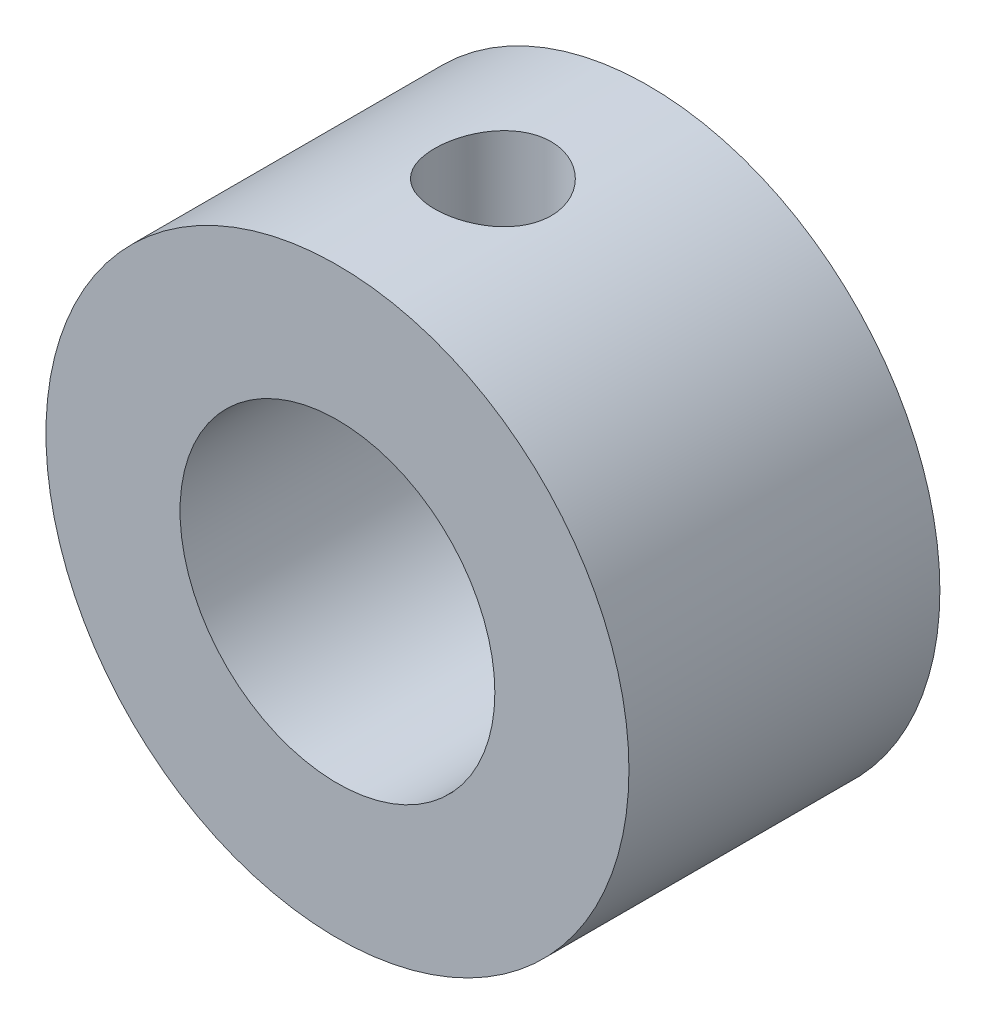
SolidWorks part; units mm, degrees
ref_plane "Plan de face" through (0, 0, 0) normal (0, 0, 1) x (1, 0, 0)
ref_plane "Plan de dessus" through (0, 0, 0) normal (0, 1, 0) x (1, 0, 0)
ref_plane "Plan de droite" through (0, 0, 0) normal (1, 0, 0) x (0, 0, -1)
sketch "Esquisse1" plane through (0, 0, 0) normal (0, 0, 1) x (1, 0, 0)
  circle A0 centre (0, 0) radius 7.5
  circle A1 centre (0, 0) radius 4.05
  dimension "D1" = 8.1
  dimension "D2" = 15
extrude "Boss.-Extru.1" add sketch "Esquisse1" along normal blind 8
ref_plane "Plan1" through (0, 7.5, 0) normal (0, 1, 0) x (1, 0, 0)
sketch "Esquisse2" plane through (0, 7.5, 0) normal (0, 1, 0) x (1, 0, 0)
  line L0 (0, 0) -> (0, -8) construction
  line L1 (-7.5, -8) -> (7.5, -8) construction
  circle A0 centre (0, -4) radius 1.5
  dimension "D1" = 3
extrude "Enlèv. mat.-Extru.1" cut sketch "Esquisse2" against normal up to next
